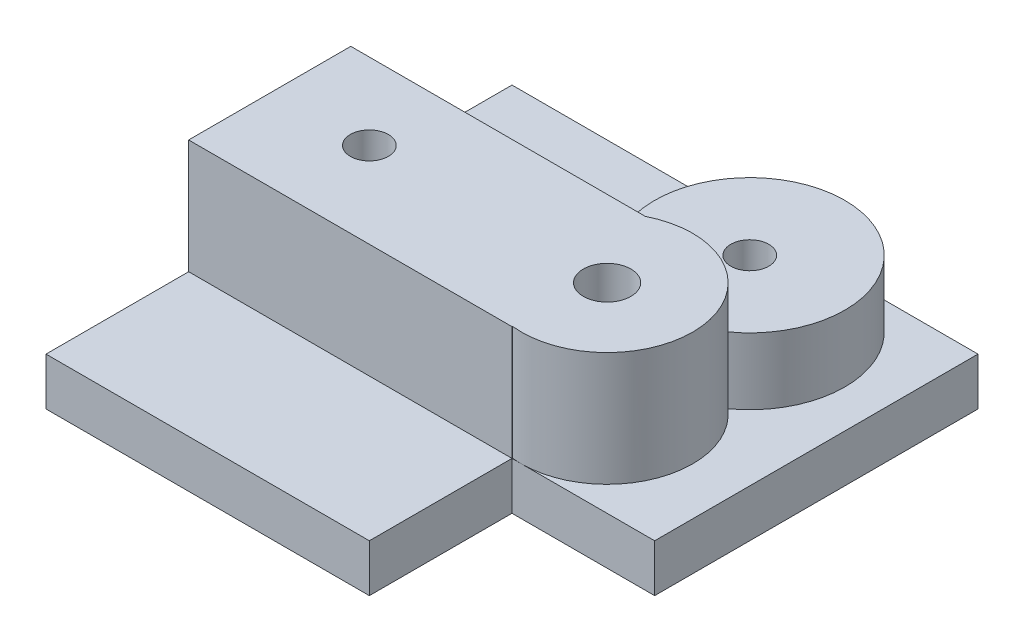
SolidWorks part; units mm, degrees
ref_plane "Front Plane" through (0, 0, 0) normal (0, 0, 1) x (1, 0, 0)
ref_plane "Top Plane" through (0, 0, 0) normal (0, 1, 0) x (1, 0, 0)
ref_plane "Right Plane" through (0, 0, 0) normal (1, 0, 0) x (0, 0, -1)
sketch "Sketch1" plane through (0, 0, 0) normal (0, 1, 0) x (1, 0, 0)
  line L1 (0, 0) -> (49, 0)
  line L2 (0, 0) -> (0, 49)
  line L3 (0, 49) -> (49, 49)
  line L4 (49, 0) -> (49, 49)
  line L5 (49, 0) -> (34, 0)
  line L6 (49, 0) -> (49, 15)
  line L7 (49, 15) -> (34, 15)
  line L8 (34, 0) -> (34, 15)
  circle A0 centre (10, 39) radius 2
  circle A1 centre (35, 39) radius 2
  circle A2 centre (10, 24) radius 2
  circle A3 centre (35, 24) radius 2.5
  dimension "D5" = 4
  dimension "D6" = 4
  dimension "D10" = 4
  dimension "D12" = 5
  dimension "D1" = 49
  dimension "D2" = 49
  dimension "D3" = 10
  dimension "D4" = 10
  dimension "D7" = 25
  dimension "D8" = 15
  dimension "D9" = 15
  dimension "D11" = 15
extrude "Boss-Extrude1" add sketch "Sketch1" along normal blind 5 contours L1 L8 L7 L4 L3 L2 A3 A2 A1 A0
sketch "Sketch2" plane through (0, 5, 0) normal (0, 1, 0) x (1, 0, 0)
  circle A0 centre (10, 39) radius 4
  dimension "D1" = 8
extrude "Cut-Extrude1" cut sketch "Sketch2" against normal blind 2
sketch "Sketch3" plane through (0, 5, 0) normal (0, 1, 0) x (1, 0, 0)
  circle A0 centre (35, 39) radius 10
extrude "Boss-Extrude2" add sketch "Sketch3" along normal blind 12
sketch "Sketch4" plane through (0, 5, 0) normal (0, -1, 0) x (1, 0, 0)
  circle A0 centre (35, -39) radius 2
extrude "Cut-Extrude2" cut sketch "Sketch4" against normal blind 12
sketch "Sketch5" plane through (0, 17, 0) normal (0, 1, 0) x (1, 0, 0)
  circle A0 centre (35, 39) radius 2
  circle A1 centre (35, 39) radius 10
extrude "Cut-Extrude3" cut sketch "Sketch5" against normal blind 5
sketch "Sketch6" plane through (0, 5, 0) normal (0, 1, 0) x (1, 0, 0)
  circle A0 centre (35, 24) radius 2.5
  circle A1 centre (35, 24) radius 9
extrude "Boss-Extrude3" add sketch "Sketch6" along normal blind 12
sketch "Sketch7" plane through (0, 5, 0) normal (0, 1, 0) x (1, 0, 0)
  line L0 (0, 0) -> (0, 49) construction
  line L1 (34, 15) -> (0, 15)
  line L2 (34, 15) -> (34, 32.0498)
  line L3 (34, 32.0498) -> (0, 32.0498)
  line L4 (0, 15) -> (0, 32.0498)
  circle A0 centre (10, 24) radius 2
  circle A1 centre (35, 24) radius 2.2997
extrude "Boss-Extrude4" add sketch "Sketch7" along normal blind 12 contours A1 | A0 | L2 L3 L4 L1
sketch "Sketch9" plane through (0, 17, 0) normal (0, 1, 0) x (1, 0, 0)
  circle A0 centre (35, 24) radius 2.5
extrude "Cut-Extrude5" cut sketch "Sketch9" against normal blind 27
